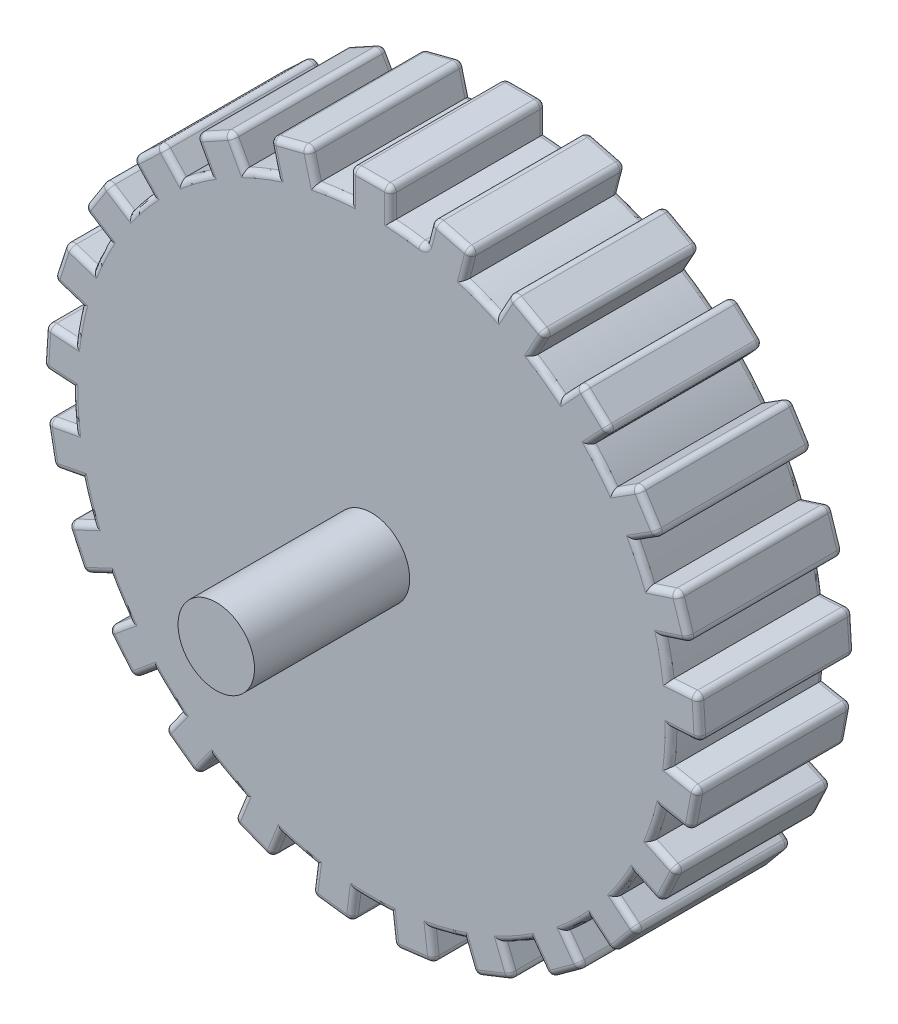
SolidWorks part; units mm, degrees
ref_plane "Front Plane" through (0, 0, 0) normal (0, 0, 1) x (1, 0, 0)
ref_plane "Top Plane" through (0, 0, 0) normal (0, 1, 0) x (1, 0, 0)
ref_plane "Right Plane" through (0, 0, 0) normal (1, 0, 0) x (0, 0, -1)
sketch "Sketch1" plane through (0, 0, 0) normal (0, 0, 1) x (1, 0, 0)
  line L1 (0, 8.5918) -> (-0.5664, 8.5918)
  line L2 (0, 8.5918) -> (0.499, 8.5918)
  line L3 (0.499, 8.5918) -> (0.499, 7.8288)
  line L5 (-0.5664, 7.8242) -> (-0.5664, 8.5918)
  arc A0 (-0.5664, 7.8242) -> (0.499, 7.8288) centre (0, 0) ccw
  point P1 (0, 8.5918)
extrude "Boss-Extrude4" add sketch "Sketch1" along normal blind 4.064
pattern_circular "CirPattern4" count 25 over 360 about axis through (0, 0, 0) along (0, 0, 1) of "Boss-Extrude4"
fillet "Fillet5" radius 0.1524 251 edges at (1.3972, 7.7192, 2.032) (-2.1694, 8.3135, 0) (-1.6534, 8.4459, 2.032) (-2.5899, 7.8092, 0) (-2.6853, 8.181, 2.032) (-1.5585, 8.0764, 0) (-5.9061, 6.2401, 0) (-5.5178, 6.6047, 2.032) (-6.0317, 5.5956, 0) (-6.2944, 5.8754, 2.032) (-5.2566, 6.3266, 0) (-8.1817, 2.6229, 0) (-8.0171, 3.1295, 2.032) (-7.9813, 1.9977, 0) (-8.3463, 2.1163, 2.032) (-7.6543, 3.0116, 0) (-8.4333, -1.6431, 0) (-8.5331, -1.1198, 2.032) (-7.9565, -2.0944, 0) (-8.3335, -2.1663, 2.032) (-8.1583, -1.0483, 0) (-6.5986, -5.5026, 0) (-6.9381, -5.0922, 2.032) (-5.9633, -5.6684, 0) (-6.259, -5.9131, 2.032) (-6.6442, -4.849, 0) (-3.1315, -8.0009, 0) (-3.6268, -7.8048, 2.032) (-2.4949, -7.8401, 0) (-2.6362, -8.197, 2.032) (-3.4863, -7.45, 0) (1.1103, -8.5198, 0) (0.5818, -8.5866, 2.032) (1.5907, -8.0723, 0) (1.6388, -8.4531, 2.032) (0.534, -8.2081, 0) (-0.5664, 8.208, 4.064) (5.0774, -6.9311, 0) (4.6465, -7.2442, 2.032) (5.2828, -6.3075, 0) (5.5084, -6.618, 2.032) (4.4222, -6.9355, 0) (7.7885, -3.6277, 0) (7.5616, -4.1097, 2.032) (7.668, -2.9823, 0) (8.0153, -3.1457, 2.032) (7.2164, -3.9472, 0) (8.5727, 0.5732, 0) (8.6062, 0.0415, 2.032) (8.1562, 1.0807, 0) (8.5393, 1.1048, 2.032) (8.2254, 0.0176, 0) (7.2362, 4.6322, 0) (7.5216, 4.1824, 2.032) (6.6267, 4.8763, 0) (6.9508, 5.082, 2.032) (7.1995, 3.978, 0) (4.1096, 7.5453, 0) (4.5764, 7.2887, 2.032) (3.4579, 7.4656, 0) (3.6428, 7.8019, 2.032) (4.3926, 6.9543, 0) (2.104, 8.3303, 0) (2.62, 8.1978, 2.032) (1.4926, 8.091, 0) (1.5881, 8.4627, 2.032) (2.5251, 7.8283, 0) (5.8569, 6.2862, 0) (6.2452, 5.9216, 2.032) (5.2058, 6.3711, 0) (5.4686, 6.6509, 2.032) (5.984, 5.6435, 0) (8.1609, 2.6871, 0) (8.3255, 2.1805, 2.032) (7.6312, 3.0751, 0) (7.9962, 3.1937, 2.032) (7.9626, 2.0626, 0) (8.4459, -1.5768, 0) (8.3461, -2.1001, 2.032) (8.1687, -0.9816, 0) (8.5457, -1.0535, 2.032) (7.9714, -2.0286, 0) (6.6416, -5.4506, 0) (6.302, -5.8611, 2.032) (6.6854, -4.7955, 0) (6.9811, -5.0402, 2.032) (6.0081, -5.6179, 0) (3.1942, -7.976, 0) (2.6989, -8.1721, 2.032) (3.5482, -7.4231, 0) (3.6895, -7.7799, 2.032) (2.5585, -7.8174, 0) (-1.0434, -8.5283, 0) (-1.5719, -8.4615, 2.032) (-0.4668, -8.2143, 0) (-0.5149, -8.595, 2.032) (-1.524, -8.083, 0) (-5.0228, -6.9707, 0) (-5.4538, -6.6576, 2.032) (-4.3663, -6.9733, 0) (-4.5919, -7.2838, 2.032) (-5.2295, -6.349, 0) (-7.7597, -3.6887, 0) (-7.9865, -3.2067, 2.032) (-7.1856, -4.0073, 0) (-7.5329, -4.1707, 2.032) (-7.6413, -3.0443, 0) (-8.577, 0.5058, 0) (-8.5435, 1.0375, 2.032) (-8.2274, -0.0499, 0) (-8.6104, -0.0258, 2.032) (-8.1627, 1.0135, 0) (-7.2724, 4.5752, 0) (-6.9869, 5.025, 2.032) (-7.2337, 3.9198, 0) (-7.5578, 4.1255, 2.032) (-6.6648, 4.8206, 0) (-4.1687, 7.5128, 0) (-3.7019, 7.7694, 2.032) (-4.4506, 6.9198, 0) (-4.6355, 7.2562, 2.032) (-3.5181, 7.4351, 0) (-1.0167, 7.7785, 4.064) (-2.9192, 7.2813, 0) (-4.6383, 6.3265, 0) (-6.0659, 4.9743, 0) (-7.1124, 3.3095, 0) (-7.712, 1.4367, 0) (-7.827, -0.5263, 0) (0.499, 8.2103, 4.064) (-7.4502, -2.4563, 0) (-6.6053, -4.2319, 0) (-5.3453, -5.7416, 0) (-3.7495, -6.8905, 0) (-1.9181, -7.6065, 0) (0.0338, -7.8446, 0) (1.9836, -7.5897, 0) (3.8088, -6.858, 0) (5.3946, -5.6953, 0) (6.6415, -4.1748, 0) (7.4711, -2.3919, 0) (7.8312, -0.4588, 0) (7.6993, 1.5031, 0) (7.0836, 3.3707, 0) (6.0228, 5.0264, 0) (4.5836, 6.3663, 0) (2.8563, 7.3061, 0) (0.9496, 7.787, 0) (-2.9192, 7.2813, 4.064) (-4.6383, 6.3265, 4.064) (-6.0659, 4.9743, 4.064) (-7.1124, 3.3095, 4.064) (-7.712, 1.4367, 4.064) (-7.827, -0.5263, 4.064) (-7.4502, -2.4563, 4.064) (-6.6053, -4.2319, 4.064) (-5.3453, -5.7416, 4.064) (-3.7495, -6.8905, 4.064) (-1.9181, -7.6065, 4.064) (0.0338, -7.8446, 4.064) (1.9836, -7.5897, 4.064) (3.8088, -6.858, 4.064) (5.3946, -5.6953, 4.064) (6.6415, -4.1748, 4.064) (7.4711, -2.3919, 4.064) (7.8312, -0.4588, 4.064) (7.6993, 1.5031, 4.064) (7.0836, 3.3707, 4.064) (6.0228, 5.0264, 4.064) (4.5836, 6.3663, 4.064) (2.8563, 7.3061, 4.064) (0.9496, 7.787, 4.064) (-0.0337, 8.5918, 4.064) (0.499, 8.2103, 0) (-1.0167, 7.7785, 0) (-0.5664, 8.208, 0) (-0.0337, 8.5918, 0) (7.9626, 2.0626, 4.064) (8.1609, 2.6871, 4.064) (7.6312, 3.0751, 4.064) (7.1995, 3.978, 4.064) (7.2362, 4.6322, 4.064) (6.6267, 4.8763, 4.064) (5.984, 5.6435, 4.064) (5.8569, 6.2862, 4.064) (5.2058, 6.3711, 4.064) (4.3926, 6.9543, 4.064) (4.1096, 7.5453, 4.064) (3.4579, 7.4656, 4.064) (2.5251, 7.8283, 4.064) (2.104, 8.3303, 4.064) (1.4926, 8.091, 4.064) (-1.5585, 8.0764, 4.064) (-2.1694, 8.3135, 4.064) (-2.5899, 7.8092, 4.064) (-3.5181, 7.4351, 4.064) (-4.1687, 7.5128, 4.064) (-4.4506, 6.9198, 4.064) (-5.2566, 6.3266, 4.064) (-5.9061, 6.2401, 4.064) (-6.0317, 5.5956, 4.064) (-6.6648, 4.8206, 4.064) (-7.2724, 4.5752, 4.064) (-7.2337, 3.9198, 4.064) (-7.6543, 3.0116, 4.064) (-8.1817, 2.6229, 4.064) (-7.9813, 1.9977, 4.064) (-8.1627, 1.0135, 4.064) (-8.577, 0.5058, 4.064) (-8.2274, -0.0499, 4.064) (-8.1583, -1.0483, 4.064) (-8.4333, -1.6431, 4.064) (-7.9565, -2.0944, 4.064) (-7.6413, -3.0443, 4.064) (-7.7597, -3.6887, 4.064) (-7.1856, -4.0073, 4.064) (-6.6442, -4.849, 4.064) (-6.5986, -5.5026, 4.064) (-5.9633, -5.6684, 4.064) (-5.2295, -6.349, 4.064) (-5.0228, -6.9707, 4.064) (-4.3663, -6.9733, 4.064) (-3.4863, -7.45, 4.064) (-3.1315, -8.0009, 4.064) (-2.4949, -7.8401, 4.064) (-1.524, -8.083, 4.064) (-1.0434, -8.5283, 4.064) (-0.4668, -8.2143, 4.064) (0.534, -8.2081, 4.064) (1.1103, -8.5198, 4.064) (1.5907, -8.0723, 4.064) (2.5585, -7.8174, 4.064) (3.1942, -7.976, 4.064) (3.5482, -7.4231, 4.064) (4.4222, -6.9355, 4.064) (5.0774, -6.9311, 4.064) (5.2828, -6.3075, 4.064) (6.0081, -5.6179, 4.064) (6.6416, -5.4506, 4.064) (6.6854, -4.7955, 4.064) (7.2164, -3.9472, 4.064) (7.7885, -3.6277, 4.064) (0.499, 8.5918, 2.032) (7.668, -2.9823, 4.064) (7.9714, -2.0286, 4.064) (8.4459, -1.5768, 4.064) (8.1687, -0.9816, 4.064) (8.2254, 0.0176, 4.064) (8.5727, 0.5732, 4.064) (8.1562, 1.0807, 4.064) (-0.5664, 8.5918, 2.032)
sketch "Sketch5" plane through (0, 0, 4.064) normal (0, 0, 1) x (1, 0, 0)
  circle A0 centre (0, 0) radius 1.0009
extrude "Boss-Extrude5" add sketch "Sketch5" along normal blind 4.064
sketch "Sketch6" plane through (0, 0, 0) normal (0, 0, -1) x (-1, 0, 0)
  circle A0 centre (0, 0) radius 0.983
extrude "Boss-Extrude6" add sketch "Sketch6" along normal blind 4.064
